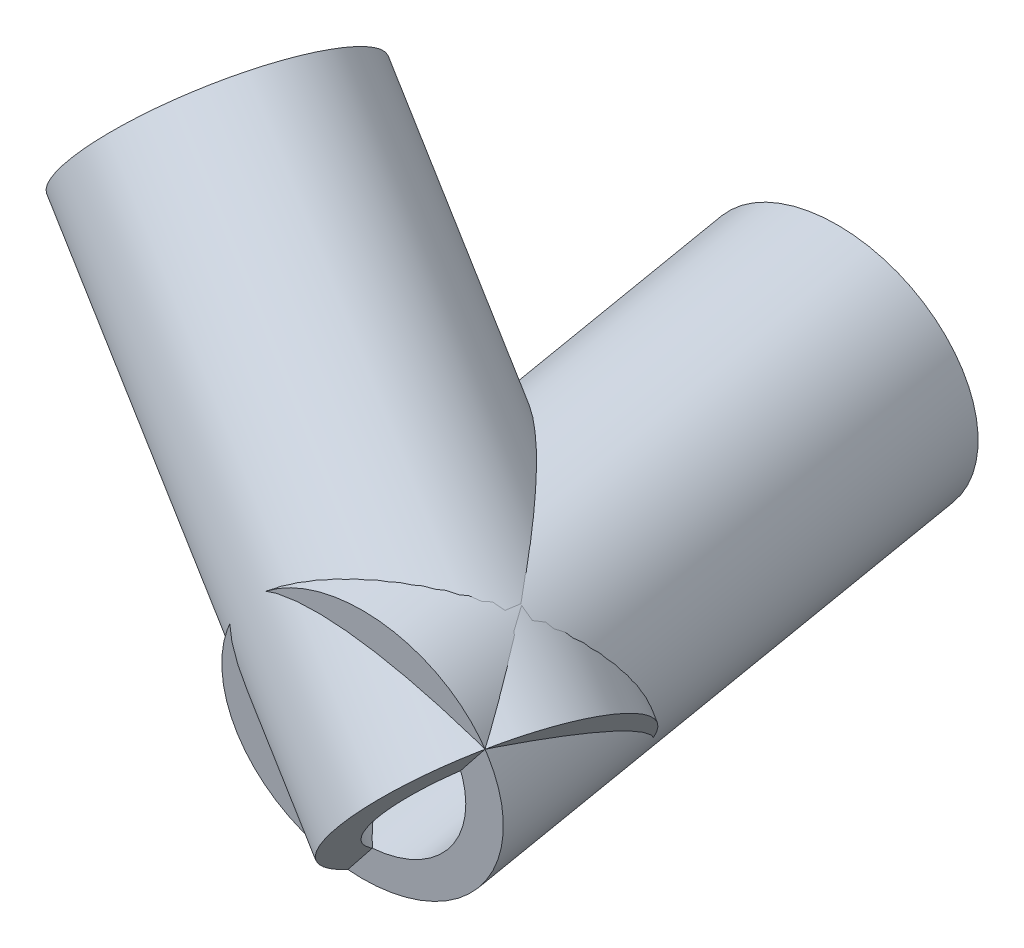
SolidWorks part; units mm, degrees
ref_plane "Front Plane" through (0, 0, 0) normal (0, 0, 1) x (1, 0, 0)
ref_plane "Top Plane" through (0, 0, 0) normal (0, 1, 0) x (1, 0, 0)
ref_plane "Right Plane" through (0, 0, 0) normal (1, 0, 0) x (0, 0, -1)
sketch "Sketch1" plane through (0, 0, 0) normal (0, 1, 0) x (1, 0, 0)
  line L0 (-33.725, 0) -> (-64.085, 378.1646) construction
  line L1 (33.725, 0) -> (64.085, 378.1646) construction
  line L2 (0, 447.6716) -> (0, -132.3407) construction
  point P2 (0, 210.7009)
  point P5 (-28.7712, 0)
  point P6 (0, 0)
  point P7 (0, 0)
  point P8 (-45.1689, 179.4431)
  point P10 (-55.3665, 269.567)
  point P11 (-64.085, 378.1646)
  point P12 (5.9869, 296.0043)
  point P13 (0, 447.6716)
  point P14 (0, -132.3407)
  point P17 (33.725, 0)
  point P18 (-33.725, 0)
  point P19 (0, 0)
  point P20 (0, 0)
  point P21 (0, 0)
  dimension "D1" = 4.59
  dimension "D2" = 33.725
  dimension "D3" = 33.725
ref_plane "Plane1" through (-33.509, 0, 2.6902) normal (0.9968, 0, -0.08) x (-0.08, 0, -0.9968)
sketch "Sketch5" plane through (-33.509, 0, 2.6902) normal (0.9968, 0, -0.08) x (-0.08, 0, -0.9968)
  line L0 (2.6988, 0) -> (386.6928, 40.8338) construction
  line L1 (2.6988, 0) -> (382.0802, 0) construction
  dimension "D1" = 6.07
sketch "Sketch7" plane through (0, 0, 0) normal (0, 1, 0) x (1, 0, 0)
  line L0 (-33.725, 0) -> (-262.8941, 71.8612) construction
  line L1 (-33.725, 0) -> (-64.085, 378.1646) construction
  point P3 (-248.3866, 107.7168)
  dimension "D1" = 68
ref_plane "Plane3" through (-3.0192, 0, 9.6285) normal (0.2992, 0, -0.9542) x (-0.9542, 0, -0.2992)
sketch "Sketch9" plane through (-3.0192, 0, 9.6285) normal (0.2992, 0, -0.9542) x (-0.9542, 0, -0.2992)
  line L0 (32.18, 0) -> (222.1342, 147.8753) construction
  line L1 (32.18, 0) -> (272.3518, 0) construction
  dimension "D1" = 37.9
sketch "Sketch12" plane through (-33.509, 0, 2.6902) normal (0.9968, 0, -0.08) x (-0.08, 0, -0.9968)
  line L0 (2.6988, 0) -> (0.8884, 17.0247) construction
  line L1 (2.6988, 0) -> (386.6928, 40.8338) construction
  line L2 (1.1127, 14.9159) -> (50.8324, 20.2031)
  line L3 (50.8324, 20.2031) -> (51.2553, 16.2255)
  line L4 (51.2553, 16.2255) -> (1.5357, 10.9383)
  line L6 (1.1127, 14.9159) -> (-8.8312, 13.8585)
  line L7 (-8.8312, 13.8585) -> (-8.4083, 9.8809)
  line L8 (-8.4083, 9.8809) -> (1.5357, 10.9383)
  dimension "D1" = 4
  dimension "D2" = 11
  dimension "D3" = 10
  dimension "D4" = 50
revolve "Revolve3" add sketch "Sketch12" angle 360 about L0
sketch "Sketch11" plane through (-3.0192, 0, 9.6285) normal (0.2992, 0, -0.9542) x (-0.9542, 0, -0.2992)
  line L0 (32.18, 0) -> (70.2683, -48.9266) construction
  line L1 (32.18, 0) -> (222.1342, 147.8753) construction
  line L2 (41.3943, -11.8363) -> (80.8485, 18.878)
  line L3 (80.8485, 18.878) -> (78.3913, 22.0343)
  line L4 (78.3913, 22.0343) -> (38.9534, -8.6672)
  line L6 (41.3943, -11.8363) -> (33.5034, -17.9791)
  line L7 (33.5034, -17.9791) -> (31.0463, -14.8228)
  line L8 (31.0463, -14.8228) -> (38.9534, -8.6672)
  dimension "D1" = 11
  dimension "D2" = 4
  dimension "D3" = 50
  dimension "D4" = 10
revolve "Revolve2" add sketch "Sketch11" angle 360 about L0
